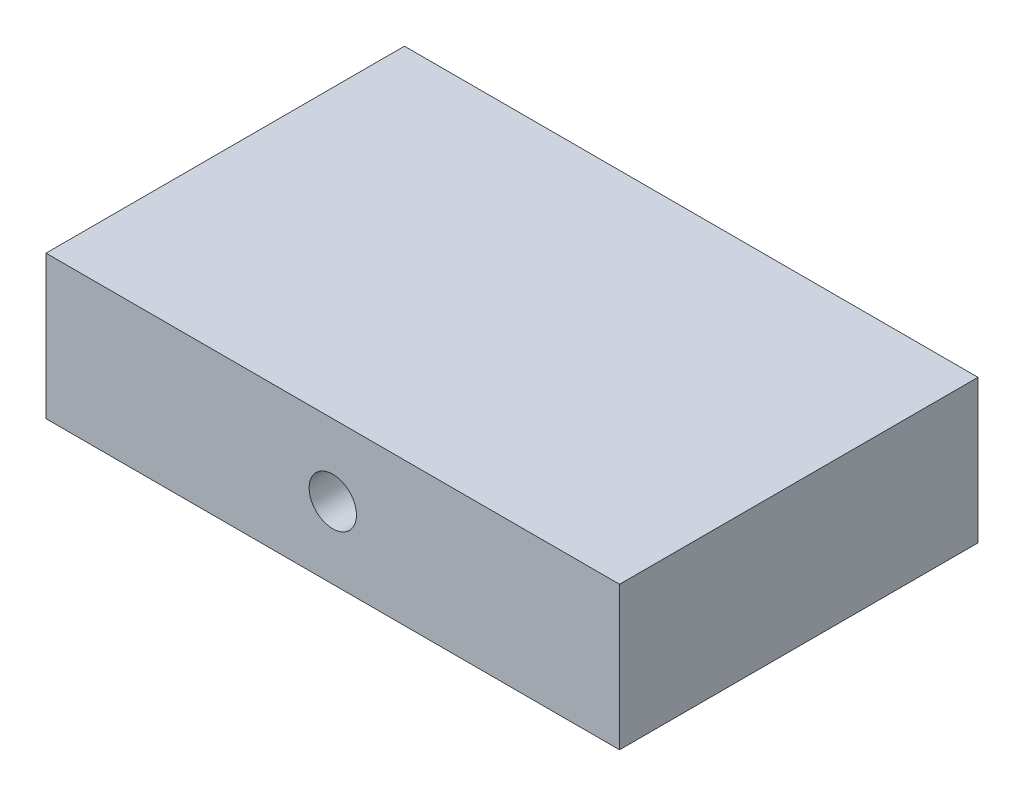
SolidWorks part; units mm, degrees
ref_plane "Front Plane" through (0, 0, 0) normal (0, 0, 1) x (1, 0, 0)
ref_plane "Top Plane" through (0, 0, 0) normal (0, 1, 0) x (1, 0, 0)
ref_plane "Right Plane" through (0, 0, 0) normal (1, 0, 0) x (0, 0, -1)
sketch "Sketch1" plane through (0, 0, 0) normal (0, 0, 1) x (1, 0, 0)
  line L1 (0, 0) -> (40, 0)
  line L2 (0, 0) -> (0, 10)
  line L3 (0, 10) -> (40, 10)
  line L4 (40, 0) -> (40, 10)
  dimension "D1" = 10
  dimension "D2" = 40
extrude "Boss-Extrude1" add sketch "Sketch1" along normal blind 25
sketch "Sketch2" plane through (0, 0, 25) normal (0, 0, 1) x (1, 0, 0)
  line L0 (0, 5) -> (40, 5) construction
  line L1 (0, 10) -> (0, 0) construction
  line L2 (40, 0) -> (40, 10) construction
  line L3 (20, 10) -> (20, 0) construction
  line L4 (40, 10) -> (0, 10) construction
  line L5 (0, 0) -> (40, 0) construction
  point P12 (20, 5)
hole_wizard "M4 Tapped Hole1" positions "3DSketch1" profile "Sketch3" tap size "M4" standard "DIN"
sketch3d "3DSketch1"
  point P0 (20, 5, 25)
cosmetic thread "Hole Thread1" parameters "D1"=6, "D2"=4
sketch "Sketch3" plane through (20, 5, 25) normal (1, 0, 0) x (0, -1, 0)
  line L0 (0, 0) -> (0, 10.4914)
  line L1 (0, 10.4914) -> (1.65, 9.5)
  line L2 (1.65, 9.5) -> (1.65, 0)
  line L5 (1.65, 0) -> (0, 0)
  line L10 (0, 10.4914) -> (-1.65, 9.5) construction
  line L11 (0, -6.35) -> (0, 107.95) construction
  dimension "Tap Drill Dia." = 3.3
  dimension "Tap Drill Depth" = 9.5
  dimension "Drill Angle" = 118
